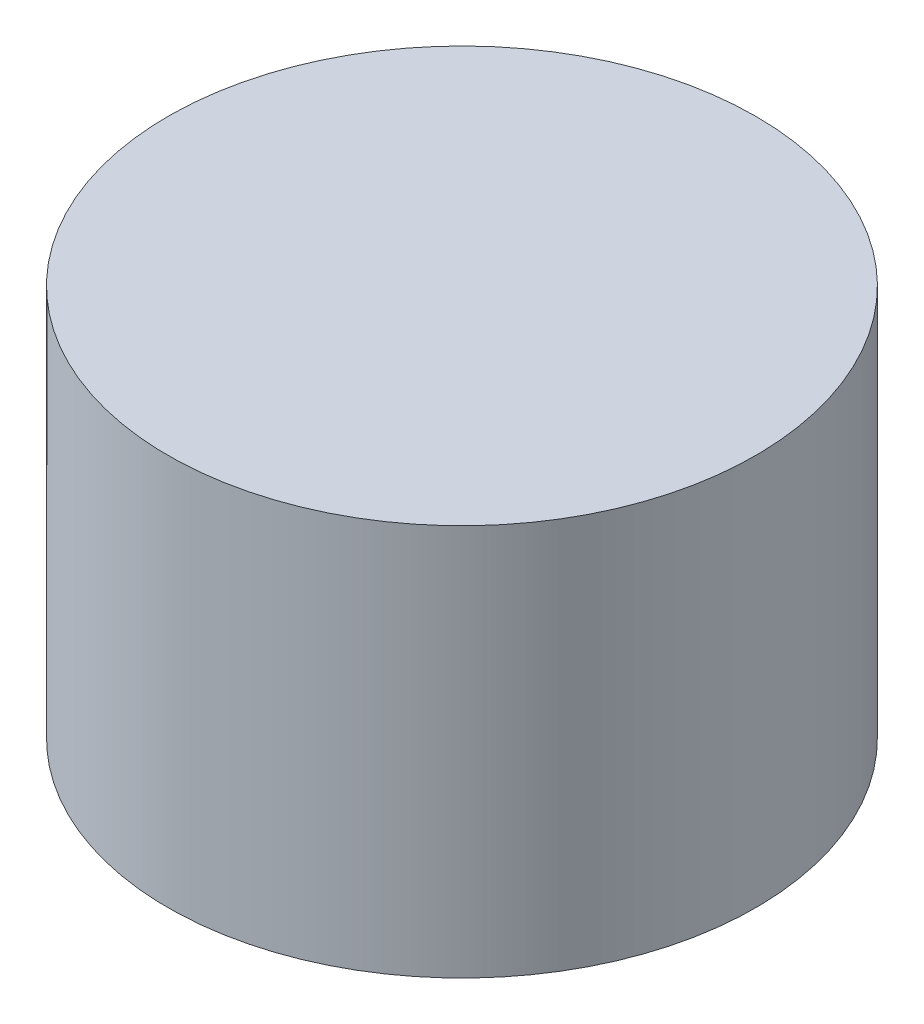
SolidWorks part; units mm, degrees
ref_plane "Plano frontal" through (0, 0, 0) normal (0, 0, 1) x (1, 0, 0)
ref_plane "Plano superior" through (0, 0, 0) normal (0, 1, 0) x (1, 0, 0)
ref_plane "Plano direito" through (0, 0, 0) normal (1, 0, 0) x (0, 0, -1)
sketch "Esboço1" plane through (0, 0, 0) normal (0, 0, 1) x (1, 0, 0)
  line L0 (0, 0) -> (0, 606.3063) construction
  line L1 (0, 0) -> (718.9894, 0) construction
  line L2 (0, 200) -> (150, 200)
  line L3 (150, 200) -> (150, 0)
  line L4 (150, 0) -> (0, 0)
  line L5 (0, 0) -> (0, 200)
  dimension "D1" = 200
  dimension "D2" = 300
revolve "Revolução1" add sketch "Esboço1" angle 360 about L0
